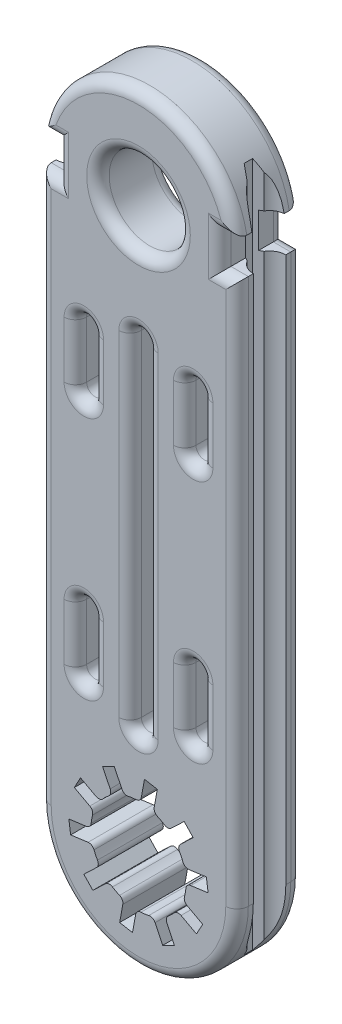
SolidWorks part; units mm, degrees
ref_plane "Alzado" through (0, 0, 0) normal (0, 0, 1) x (1, 0, 0)
ref_plane "Planta" through (0, 0, 0) normal (0, 1, 0) x (1, 0, 0)
ref_plane "Vista lateral" through (0, 0, 0) normal (1, 0, 0) x (0, 0, -1)
sketch "Croquis1" plane through (0, 0, 0) normal (0, 0, 1) x (1, 0, 0)
  line L0 (-0.0916, 52.5612) -> (5.6575, 52.5612)
  line L1 (11.6575, 52.5612) -> (17.4066, 52.5612)
  arc A0 (5.6575, 52.5612) -> (11.6575, 52.5612) centre (8.6575, 52.5612) ccw
  arc A1 (-0.0916, 52.5612) -> (17.4066, 52.5612) centre (8.6575, 52.5612) ccw
extrude "Saliente-Extruir1" add sketch "Croquis1" along normal blind 3 and the other way blind 2.78
sketch "Croquis2" plane through (0, 52.5612, 0) normal (0, 1, 0) x (1, 0, 0)
  line L0 (1.7903, -0.1147) -> (-0.0916, -0.1147) construction
  line L1 (-0.0916, -3) -> (17.4066, -3)
  line L5 (-0.0916, -3) -> (-0.0916, 2.78) construction
  line L6 (-0.0916, 2.7705) -> (-0.0916, -3)
  line L7 (8.6575, -3) -> (8.6575, 4.706) construction
  line L8 (17.4066, 2.7705) -> (17.4066, -3)
  line L9 (-0.0916, 2.7705) -> (17.4066, 2.7705)
extrude "Saliente-Extruir2" add sketch "Croquis2" along normal blind 50
sketch "Croquis4" plane through (0, 0, 3) normal (0, 0, 1) x (1, 0, 0)
  line L0 (-0.0916, 102.5612) -> (17.4066, 102.5612) construction
  circle A0 centre (8.6575, 102.5612) radius 8.7491
extrude "Saliente-Extruir3" add sketch "Croquis4" against normal through all
sketch "Croquis5" plane through (0, 0, 3) normal (0, 0, 1) x (1, 0, 0)
  line L0 (-0.0916, 77.5612) -> (17.4066, 77.5612) construction
  line L3 (5.6575, 52.5612) -> (11.6575, 52.5612) construction
  circle A1 centre (8.6575, 102.5612) radius 3.6
  circle A2 centre (8.6575, 52.5612) radius 3.15
extrude "Cortar-Extruir1" cut sketch "Croquis5" against normal blind 12
sketch "Croquis6" plane through (0, 0, -2.78) normal (0, 0, -1) x (-1, 0, 0)
  line L0 (-1.4566, 104.0883) -> (0.6816, 104.0883)
  line L1 (-1.4566, 104.0883) -> (-1.4566, 100.981)
  line L2 (-1.4566, 100.981) -> (0.6816, 100.981)
  line L3 (0.6816, 100.981) -> (0.6816, 104.0883)
  line L4 (-8.6575, 106.1612) -> (-8.6575, 98.9612) construction
  line L5 (-15.8585, 100.981) -> (-17.9967, 100.981)
  line L6 (-15.8585, 104.0883) -> (-15.8585, 100.981)
  line L7 (-15.8585, 104.0883) -> (-17.9967, 104.0883)
  line L8 (-17.9967, 100.981) -> (-17.9967, 104.0883)
  circle A0 centre (-8.6575, 102.5612) radius 3.6 construction
extrude "Cortar-Extruir2" cut sketch "Croquis6" against normal blind 9
sketch "Croquis7" plane through (0, 0, 3) normal (0, 0, 1) x (1, 0, 0)
  line L1 (13.5111, 63.9913) -> (13.5111, 68.9913) construction
  line L6 (12.7611, 63.9913) -> (12.7611, 68.9913)
  line L7 (14.2611, 63.9913) -> (14.2611, 68.9913)
  line L8 (8.6575, 77.338) -> (12.7611, 77.338) construction
  line L9 (3.804, 63.9913) -> (3.804, 68.9913) construction
  line L10 (4.554, 63.9913) -> (4.554, 68.9913)
  line L11 (3.054, 63.9913) -> (3.054, 68.9913)
  line L12 (13.5111, 90.6846) -> (13.5111, 85.6846) construction
  line L13 (12.7611, 90.6846) -> (12.7611, 85.6846)
  line L14 (14.2611, 90.6846) -> (14.2611, 85.6846)
  line L15 (3.804, 90.6846) -> (3.804, 85.6846) construction
  line L16 (4.554, 90.6846) -> (4.554, 85.6846)
  line L17 (3.054, 90.6846) -> (3.054, 85.6846)
  arc A1 (12.7611, 63.9913) -> (14.2611, 63.9913) centre (13.5111, 63.9913) ccw
  arc A2 (14.2611, 68.9913) -> (12.7611, 68.9913) centre (13.5111, 68.9913) ccw
  arc A3 (4.554, 63.9913) -> (3.054, 63.9913) centre (3.804, 63.9913) cw
  arc A4 (3.054, 68.9913) -> (4.554, 68.9913) centre (3.804, 68.9913) cw
  arc A5 (12.7611, 90.6846) -> (14.2611, 90.6846) centre (13.5111, 90.6846) cw
  arc A6 (14.2611, 85.6846) -> (12.7611, 85.6846) centre (13.5111, 85.6846) cw
  arc A7 (4.554, 90.6846) -> (3.054, 90.6846) centre (3.804, 90.6846) ccw
  arc A8 (3.054, 85.6846) -> (4.554, 85.6846) centre (3.804, 85.6846) ccw
  point P12 (13.5111, 66.4913)
  point P17 (3.804, 66.4913)
  point P24 (13.5111, 88.1846)
  point P31 (3.804, 88.1846)
extrude "Cortar-Extruir3" cut sketch "Croquis7" against normal blind 10
sketch "Croquis8" plane through (0, 0, -2.78) normal (0, 0, -1) x (-1, 0, 0)
  line L1 (-8.6575, 92.0844) -> (-8.6575, 62.338) construction
  line L2 (-7.9075, 92.0844) -> (-7.9075, 62.338)
  line L3 (-9.4075, 92.0844) -> (-9.4075, 62.338)
  arc A2 (-7.9075, 92.0844) -> (-9.4075, 92.0844) centre (-8.6575, 92.0844) ccw
  arc A3 (-9.4075, 62.338) -> (-7.9075, 62.338) centre (-8.6575, 62.338) ccw
  point P9 (-8.6575, 77.2112)
extrude "Cortar-Extruir4" cut sketch "Croquis8" against normal blind 10
sketch "Croquis9" plane through (0, 0, -2.7705) normal (0, 0, -1) x (-1, 0, 0)
  circle A0 centre (-8.6575, 52.5612) radius 63.7468
extrude "Cortar-Extruir5" cut sketch "Croquis9" along normal blind 3
fillet "Redondeo1" radius 1 64 edges at (8.6575, 111.3103, 3) (8.6575, 43.8121, -2.7705) (8.6575, 43.8121, 3) (-0.0916, 76.7711, 3) (17.4066, 76.7711, 3) (5.0575, 102.5612, 3) (5.0575, 102.5612, -2.7705) (11.8075, 52.5612, 3) (11.8075, 52.5612, -2.7705) (17.4066, 76.7711, -2.7705) (-0.0916, 76.7711, -2.7705) (16.5654, 104.0883, -2.7705) (16.5654, 104.0883, 3) (15.8585, 102.5347, -2.7705) (15.8585, 102.5347, 3) (16.6326, 100.981, -2.7705) (16.6326, 100.981, 3) (0.6825, 100.981, -2.7705) (0.6825, 100.981, 3) (1.4566, 102.5347, -2.7705) (1.4566, 102.5347, 3) (0.7497, 104.0883, -2.7705) (0.7497, 104.0883, 3) (14.2611, 66.4913, 3) (14.2611, 66.4913, -2.7705) (13.5111, 69.7413, 3) (13.5111, 69.7413, -2.7705) (12.7611, 66.4913, 3) (12.7611, 66.4913, -2.7705) (13.5111, 63.2413, 3) (13.5111, 63.2413, -2.7705) (3.054, 88.1846, 3) (3.054, 88.1846, -2.7705) (3.804, 84.9346, 3) (3.804, 84.9346, -2.7705) (4.554, 88.1846, 3) (4.554, 88.1846, -2.7705) (3.804, 91.4346, 3) (3.804, 91.4346, -2.7705) (12.7611, 88.1846, 3) (12.7611, 88.1846, -2.7705) (13.5111, 84.9346, 3) (13.5111, 84.9346, -2.7705) (14.2611, 88.1846, 3) (14.2611, 88.1846, -2.7705) (13.5111, 91.4346, 3) (13.5111, 91.4346, -2.7705) (4.554, 66.4913, 3) (4.554, 66.4913, -2.7705) (3.804, 69.7413, 3) (3.804, 69.7413, -2.7705) (3.054, 66.4913, 3) (3.054, 66.4913, -2.7705) (3.804, 63.2413, 3) (3.804, 63.2413, -2.7705) (7.9075, 77.2112, 3) (7.9075, 77.2112, -2.7705) (8.6575, 61.588, 3) (8.6575, 61.588, -2.7705) (9.4075, 77.2112, 3) (9.4075, 77.2112, -2.7705) (8.6575, 92.8344, 3) (8.6575, 92.8344, -2.7705) (8.6575, 111.3103, -2.7705)
ref_plane "Plano1" through (0, 111.3103, 0) normal (0, 1, 0) x (1, 0, 0)
sketch "Croquis10" plane through (0, 111.3103, 0) normal (0, 1, 0) x (1, 0, 0)
  line L0 (17.4066, 1.7705) -> (17.4066, -2) construction
  line L1 (15.5248, 0.2603) -> (16.1743, 0.6353)
  line L3 (16.1743, -0.8647) -> (15.5248, -0.4897)
  line L4 (15.5248, -0.4897) -> (15.5248, 0.2603)
  line L5 (-0.0916, -0.1147) -> (17.4066, -0.1147) construction
  line L6 (-0.0916, -2) -> (-0.0916, 1.7705) construction
  line L7 (8.6575, -0.1147) -> (8.6575, -0.8647) construction
  line L8 (1.1408, -0.8647) -> (1.7903, -0.4897)
  line L9 (1.7903, -0.4897) -> (1.7903, 0.2603)
  line L10 (1.7903, 0.2603) -> (1.1408, 0.6353)
  arc A0 (16.1743, -0.8647) -> (16.1743, 0.6353) centre (17.4066, -0.1147) ccw
  arc A1 (1.1408, -0.8647) -> (1.1408, 0.6353) centre (-0.0916, -0.1147) cw
extrude "Cortar-Extruir6" cut sketch "Croquis10" against normal blind 73
sketch "Croquis14" plane through (0, 0, -2.7705) normal (0, 0, -1) x (-1, 0, 0)
  line L20 (-10.0502, 56.9825) -> (-10.3291, 58.5164)
  line L21 (-10.3291, 58.5164) -> (-9.189, 58.7237)
  line L22 (-9.189, 58.7237) -> (-8.9101, 57.1898)
  line L23 (-7.1854, 56.9567) -> (-6.5094, 58.3616)
  line L24 (-6.5094, 58.3616) -> (-5.4652, 57.8591)
  line L25 (-5.4652, 57.8591) -> (-6.1412, 56.4543)
  line L26 (-4.883, 55.252) -> (-3.5103, 55.9912)
  line L27 (-3.5103, 55.9912) -> (-2.9609, 54.9709)
  line L28 (-2.9609, 54.9709) -> (-4.3335, 54.2317)
  line L29 (-4.0222, 52.5194) -> (-2.4772, 52.3107)
  line L30 (-2.4772, 52.3107) -> (-2.6324, 51.1623)
  line L31 (-2.6324, 51.1623) -> (-4.1774, 51.3711)
  line L32 (-4.9321, 49.8029) -> (-3.8049, 48.7258)
  line L33 (-3.8049, 48.7258) -> (-4.6054, 47.888)
  line L34 (-4.6054, 47.888) -> (-5.7326, 48.965)
  line L35 (-7.2649, 48.1399) -> (-6.986, 46.606)
  line L36 (-6.986, 46.606) -> (-8.1261, 46.3987)
  line L37 (-8.1261, 46.3987) -> (-8.405, 47.9326)
  line L38 (-10.1296, 48.1657) -> (-10.8057, 46.7608)
  line L39 (-10.8057, 46.7608) -> (-11.8498, 47.2633)
  line L40 (-11.8498, 47.2633) -> (-11.1738, 48.6681)
  line L41 (-12.4321, 49.8704) -> (-13.8048, 49.1312)
  line L42 (-13.8048, 49.1312) -> (-14.3542, 50.1515)
  line L43 (-14.3542, 50.1515) -> (-12.9816, 50.8907)
  line L44 (-13.2928, 52.603) -> (-14.8378, 52.8118)
  line L45 (-14.8378, 52.8118) -> (-14.6826, 53.9601)
  line L46 (-14.6826, 53.9601) -> (-13.1376, 53.7513)
  line L47 (-12.383, 55.3196) -> (-13.5102, 56.3966)
  line L48 (-13.5102, 56.3966) -> (-12.7097, 57.2344)
  line L49 (-12.7097, 57.2344) -> (-11.5825, 56.1574)
  arc A1 (-12.2976, 54.7044) -> (-12.6036, 54.0684) centre (-8.6575, 52.5612) ccw
  arc A2 (-10.3427, 56.4346) -> (-10.964, 56.1) centre (-8.6575, 52.5612) ccw
  arc A3 (-7.7441, 56.6854) -> (-8.4435, 56.7799) centre (-8.6575, 52.5612) ccw
  arc A4 (-5.4944, 55.3608) -> (-6.0047, 55.8484) centre (-8.6575, 52.5612) ccw
  arc A5 (-4.453, 52.9669) -> (-4.5792, 53.6613) centre (-8.6575, 52.5612) ccw
  arc A6 (-9.571, 48.4371) -> (-8.8716, 48.3425) centre (-8.6575, 52.5612) ccw
  arc A7 (-6.9724, 48.6878) -> (-6.351, 49.0224) centre (-8.6575, 52.5612) ccw
  arc A8 (-11.8206, 49.7616) -> (-11.3104, 49.274) centre (-8.6575, 52.5612) ccw
  arc A9 (-5.0175, 50.4181) -> (-4.7115, 51.054) centre (-8.6575, 52.5612) ccw
  arc A10 (-12.8621, 52.1555) -> (-12.7359, 51.4611) centre (-8.6575, 52.5612) ccw
  arc A11 (-10.964, 56.1) -> (-11.5825, 56.1574) centre (-11.2371, 56.5189) cw
  arc A12 (-10.3427, 56.4346) -> (-10.0502, 56.9825) centre (-10.5421, 56.8931) ccw
  arc A13 (-8.4435, 56.7799) -> (-8.9101, 57.1898) centre (-8.4182, 57.2792) cw
  arc A14 (-7.1854, 56.9567) -> (-7.7441, 56.6854) centre (-7.636, 57.1735) cw
  arc A15 (-6.0047, 55.8484) -> (-6.1412, 56.4543) centre (-5.6907, 56.2375) cw
  arc A16 (-4.883, 55.252) -> (-5.4944, 55.3608) centre (-5.12, 55.6922) cw
  arc A17 (-4.5792, 53.6613) -> (-4.3335, 54.2317) centre (-4.0965, 53.7915) cw
  arc A18 (-4.0222, 52.5194) -> (-4.453, 52.9669) centre (-3.9553, 53.0149) cw
  arc A19 (-4.7115, 51.054) -> (-4.1774, 51.3711) centre (-4.2444, 50.8756) cw
  arc A20 (-4.9321, 49.8029) -> (-5.0175, 50.4181) centre (-4.5866, 50.1644) cw
  arc A21 (-5.7326, 48.965) -> (-6.351, 49.0224) centre (-6.078, 48.6035) ccw
  arc A22 (-7.2649, 48.1399) -> (-6.9724, 48.6878) centre (-6.7729, 48.2293) cw
  arc A23 (-8.405, 47.9326) -> (-8.8716, 48.3425) centre (-8.8969, 47.8432) ccw
  arc A24 (-10.1296, 48.1657) -> (-9.571, 48.4371) centre (-9.6791, 47.9489) cw
  arc A25 (-11.1738, 48.6681) -> (-11.3104, 49.274) centre (-11.6244, 48.8849) ccw
  arc A26 (-12.4321, 49.8704) -> (-11.8206, 49.7616) centre (-12.195, 49.4302) cw
  arc A27 (-13.2928, 52.603) -> (-12.8621, 52.1555) centre (-13.3598, 52.1075) cw
  arc A28 (-12.9816, 50.8907) -> (-12.7359, 51.4611) centre (-13.2186, 51.3309) ccw
  arc A29 (-13.1376, 53.7513) -> (-12.6036, 54.0684) centre (-13.0707, 54.2468) ccw
  arc A30 (-12.2976, 54.7044) -> (-12.383, 55.3196) centre (-12.7284, 54.958) ccw
  point P36 (-7.3654, 56.5828)
  point P45 (-5.2483, 55.0552)
  point P56 (-4.4335, 52.575)
  point P60 (-8.6575, 52.5612)
  point P65 (-5.2321, 50.0895)
  point P68 (-6.0326, 49.2517)
  point P71 (-7.3391, 48.5481)
  point P74 (-8.4792, 48.3409)
  point P77 (-9.9497, 48.5396)
  point P82 (-12.0668, 50.0672)
  point P85 (-12.8816, 52.5474)
  dimension "D1" = 0.5
extrude "Cortar-Extruir7" cut sketch "Croquis14" against normal blind 8
